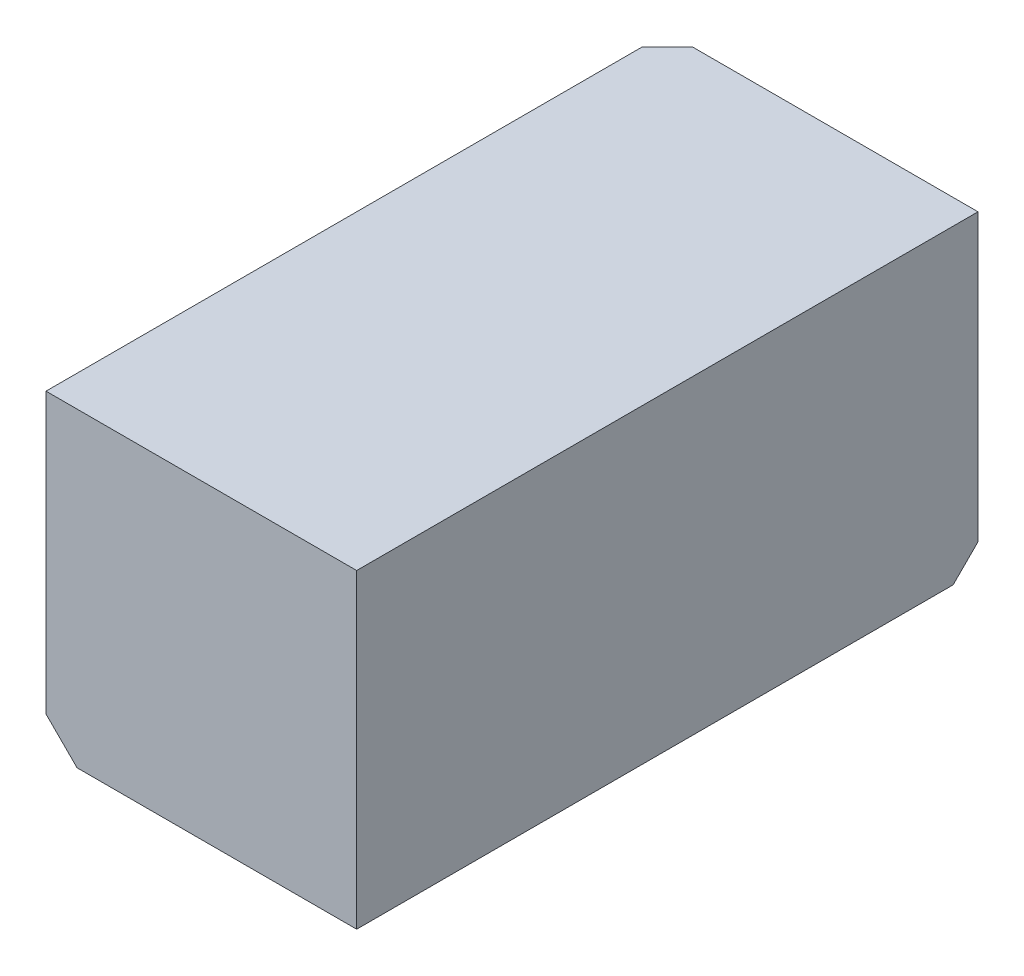
SolidWorks part; units mm, degrees
ref_plane "Front Plane" through (0, 0, 0) normal (0, 0, 1) x (1, 0, 0)
ref_plane "Top Plane" through (0, 0, 0) normal (0, 1, 0) x (1, 0, 0)
ref_plane "Right Plane" through (0, 0, 0) normal (1, 0, 0) x (0, 0, -1)
sketch "Sketch1" plane through (0, 0, 0) normal (0, 0, 1) x (1, 0, 0)
  line L0 (0, 2.5) -> (0, -2.5) construction
  line L1 (-2.5, 2.5) -> (2.5, 2.5)
  line L2 (-2.5, 2.5) -> (-2.5, -2.5)
  line L3 (-2.5, -2.5) -> (2.5, -2.5)
  line L4 (2.5, 2.5) -> (2.5, -2.5)
  dimension "D1" = 5
  dimension "D2" = 5
extrude "Boss-Extrude1" add sketch "Sketch1" along normal blind 10
sketch "Sketch3" plane through (2.5, 0, 0) normal (1, 0, 0) x (0, 0, -1)
  line L0 (-2.5, 4.5) -> (-2.5, -4.5) construction
  line L2 (-10, -2.5) -> (0, -2.5) construction
  line L4 (0, -2.5) -> (0, 2.5) construction
  circle A0 centre (-2.5, 0) radius 1.6
  dimension "D1" = 3.2
  dimension "D2" = 2.5
  dimension "D3" = 2.5
extrude "Cut-Extrude2" [suppressed] cut sketch "Sketch3" against normal blind 4.5
sketch "Sketch4" plane through (0, -2.5, 0) normal (0, -1, 0) x (1, 0, 0)
  line L0 (-2.5, 7.5) -> (2.5, 7.5) construction
  line L3 (2.5, 10) -> (2.5, 0) construction
  line L4 (-2.5, 10) -> (2.5, 10) construction
  line L5 (-2.5, 10) -> (-2.5, 0) construction
  circle A0 centre (0, 7.5) radius 1.6
  dimension "D1" = 3.2
  dimension "D2" = 2.5
  dimension "D3" = 2.5
extrude "Cut-Extrude3" cut sketch "Sketch4" against normal blind 4.5
sketch "Sketch5" plane through (-2.5, 0, 0) normal (-1, 0, 0) x (0, 0, 1)
  line L0 (0, 2.5) -> (0, -2.5) construction
  line L1 (0, 0) -> (10, 0) construction
  line L2 (10, 2.5) -> (10, -2.5) construction
  circle A0 centre (2.5, 0) radius 1.6
  dimension "D2" = 3.2
  dimension "D1" = 2.5
extrude "Cut-Extrude4" cut sketch "Sketch5" against normal blind 4.5
chamfer "Chamfer1" distance 0.5 angle 45 1 edges at (-2.5, -2.5, 5)
chamfer "Chamfer2" [suppressed] distance 0.5 angle 45
chamfer "Chamfer3" [suppressed] distance 0.4 angle 45
chamfer "Chamfer4" distance 0.4 angle 45 3 edges at (-2.5, 0.25, 0) (-2.25, -2.25, 0) (0.25, -2.5, 0)
